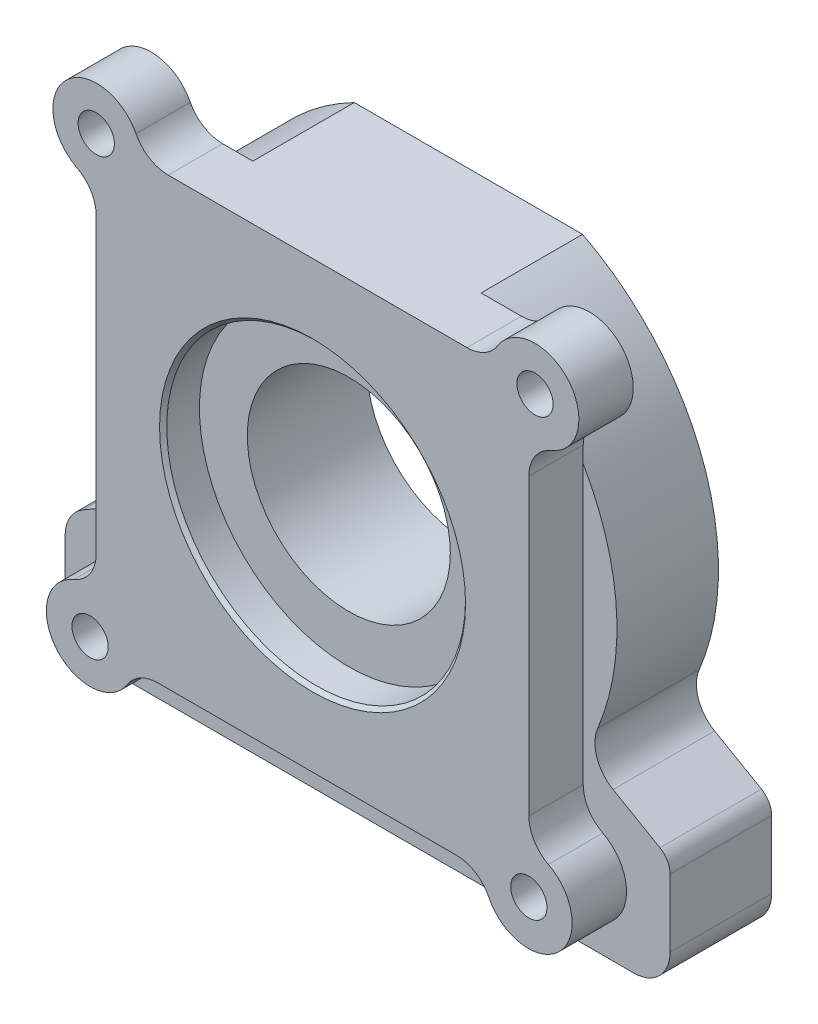
SolidWorks part; units mm, degrees
ref_plane "Front Plane" through (0, 0, 0) normal (0, 0, 1) x (1, 0, 0)
ref_plane "Top Plane" through (0, 0, 0) normal (0, 1, 0) x (1, 0, 0)
ref_plane "Right Plane" through (0, 0, 0) normal (1, 0, 0) x (0, 0, -1)
sketch "Sketch1" plane through (0, 0, 0) normal (0, 0, 1) x (1, 0, 0)
  line L0 (-60.1958, 77.9313) -> (62.7096, 77.9313)
  line L2 (-75.7753, 62.5105) -> (-75.7753, -60.3408)
  line L4 (-62.6916, -77.9313) -> (60.1994, -77.9313)
  line L5 (75.7753, 60.5535) -> (75.7753, -62.8959)
  arc A0 (75.7753, 60.5535) -> (62.7096, 77.9313) centre (77.9313, 75.7753) ccw
  arc A1 (-60.1958, 77.9313) -> (-75.7753, 62.5105) centre (-75.5694, 77.8828) ccw
  arc A2 (-75.7753, -60.3408) -> (-62.6916, -77.9313) centre (-77.8827, -75.5693) ccw
  arc A3 (60.1994, -77.9313) -> (75.7753, -62.8959) centre (75.5694, -78.2682) ccw
  circle A5 centre (77.9313, 75.7753) radius 6.35
  circle A6 centre (75.7753, -77.9313) radius 6.35
  circle A7 centre (-77.9313, -75.7753) radius 6.35
  circle A8 centre (-75.7753, 77.9313) radius 6.35
  dimension "D1" = 12.7
  dimension "D2" = 122.8512
extrude "Extrude1" add sketch "Sketch1" along normal blind 19.05
fillet "Fillet1" radius 12.7 8 edges at (-75.7753, -60.3408, 9.525) (-75.7753, 62.5105, 9.525) (-60.1958, 77.9313, 9.525) (62.7096, 77.9313, 9.525) (75.7753, 60.5535, 9.525) (75.7753, -62.8959, 9.525) (60.1994, -77.9313, 9.525) (-62.6916, -77.9313, 9.525)
sketch "Sketch2" plane through (0, 0, 19.05) normal (0, 0, 1) x (1, 0, 0)
  circle A0 centre (0, 0) radius 52.3279
  dimension "D1" = 104.6558
extrude "Cut-Extrude2" cut sketch "Sketch2" against normal blind 12.7
chamfer "Chamfer1" distance 1.27 angle 45 1 edges at (52.3279, 0, 19.05)
sketch "Sketch4" plane through (0, 0, 0) normal (0, 0, -1) x (-1, 0, 0)
  line L0 (86.09, -49.8565) -> (99.3976, -57.5632)
  line L1 (105.733, -68.5533) -> (105.733, -88.9455)
  line L2 (93.033, -101.6455) -> (-93.5216, -101.6455)
  line L3 (-106.2216, -88.9455) -> (-106.2216, -65.2337)
  line L4 (-102.6429, -59.0463) -> (-86.234, -49.6069)
  arc A0 (80.747, -33.9447) -> (-80.845, -33.7107) centre (0, 0) ccw
  arc A1 (86.09, -49.8565) -> (80.747, -33.9447) centre (92.4546, -38.8664) cw
  arc A2 (-86.234, -49.6069) -> (-80.845, -33.7107) centre (-92.5668, -38.5985) ccw
  arc A3 (-106.2216, -88.9455) -> (-93.5216, -101.6455) centre (-93.5216, -88.9455) ccw
  arc A6 (-106.2216, -65.2337) -> (-102.6429, -59.0463) centre (-99.0835, -65.2337) cw
  arc A7 (99.3976, -57.5632) -> (105.733, -68.5533) centre (93.033, -68.5533) cw
  arc A8 (105.733, -88.9455) -> (93.033, -101.6455) centre (93.033, -88.9455) cw
  dimension "D1" = 12.7
  dimension "D2" = 12.7
extrude "Extrude2" add sketch "Sketch4" along normal blind 35.56
sketch "Sketch3" plane through (0, 0, 0) normal (0, 0, 1) x (1, 0, 0)
  circle A0 centre (0, 0) radius 35.56
  dimension "D1" = 71.12
extrude "Cut-Extrude3" cut sketch "Sketch3" along normal through all and the other way through all
sketch "Sketch5" plane through (0, 0, 0) normal (0, 0, 1) x (1, 0, 0)
  line L0 (54.1106, 77.9313) -> (-50.5573, 77.9313) construction
  line L1 (-53.0702, 119.1209) -> (48.3463, 119.1209)
  line L2 (-53.0702, 119.1209) -> (-53.0702, 77.9313)
  line L3 (-53.0702, 77.9313) -> (48.3463, 77.9313)
  line L4 (48.3463, 119.1209) -> (48.3463, 77.9313)
extrude "Cut-Extrude4" cut sketch "Sketch5" against normal blind 40.64
sketch "Sketch7" plane through (0, 0, 0) normal (0, 0, 1) x (1, 0, 0)
  circle A0 centre (75.7753, -77.9313) radius 6.35
  circle A1 centre (-77.9313, -75.7753) radius 6.35
extrude "Cut-Extrude6" cut sketch "Sketch7" against normal through all
